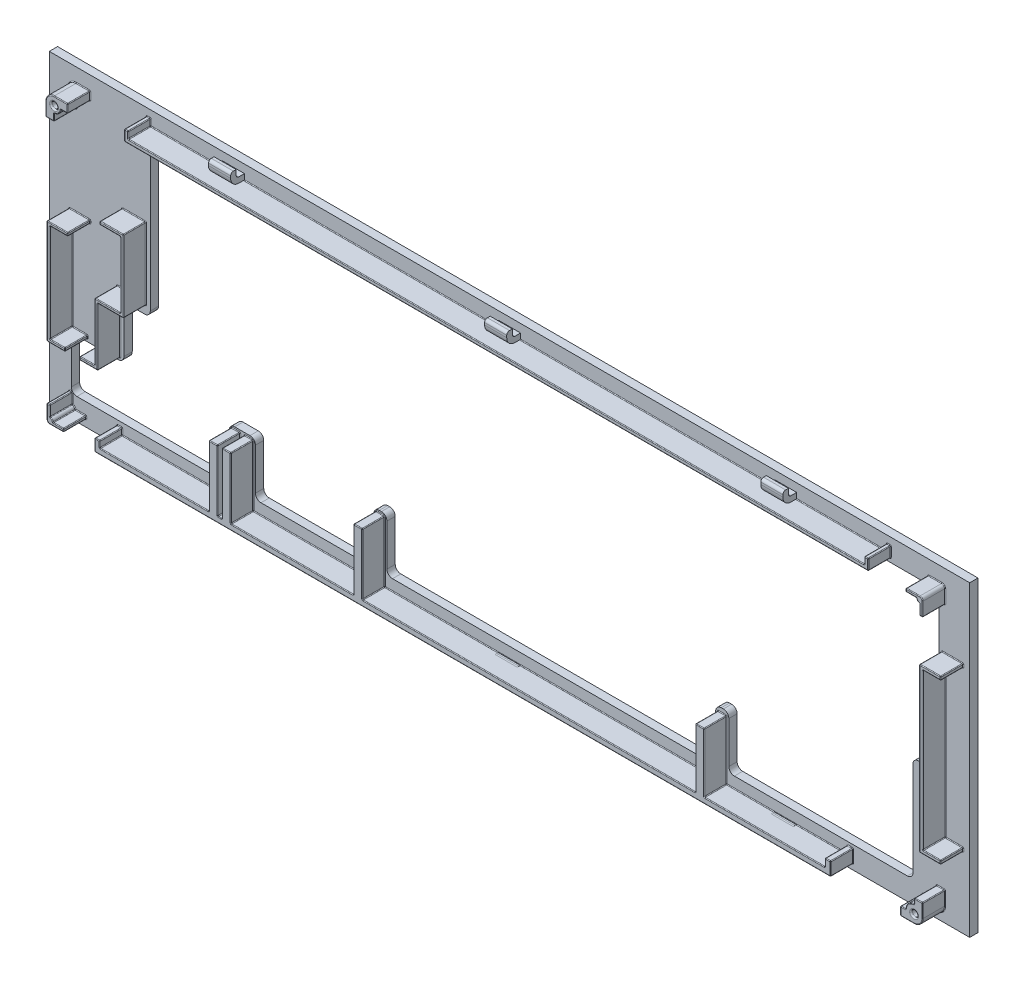
SolidWorks part; units mm, degrees
ref_plane "Front Plane" through (0, 0, 0) normal (0, 0, 1) x (1, 0, 0)
ref_plane "Top Plane" through (0, 0, 0) normal (0, 1, 0) x (1, 0, 0)
ref_plane "Right Plane" through (0, 0, 0) normal (1, 0, 0) x (0, 0, -1)
sketch "keystencil" plane through (0, 0, 0) normal (0, 0, 1) x (1, 0, 0)
  line L0 (-542.8355, 969.3624) -> (-824.5855, 969.3624)
  line L1 (-541.3355, 952.4124) -> (-541.3355, 967.2624) construction
  line L2 (-542.9355, 968.8624) -> (-557.7855, 968.8624) construction
  line L4 (-826.0855, 967.2624) -> (-826.0855, 952.4124) construction
  line L5 (-826.5855, 967.3624) -> (-826.5855, 914.2124)
  line L6 (-819.1605, 911.7124) -> (-834.0105, 911.7124) construction
  line L7 (-828.5855, 912.2124) -> (-834.1105, 912.2124)
  line L8 (-836.1105, 910.2124) -> (-836.1105, 895.1624)
  line L9 (-835.6105, 910.1124) -> (-835.6105, 895.2624) construction
  line L10 (-838.1105, 893.1624) -> (-853.1605, 893.1624)
  line L11 (-838.2105, 892.6624) -> (-853.0605, 892.6624) construction
  line L12 (-854.6605, 891.0624) -> (-854.6605, 876.2124) construction
  line L13 (-855.1605, 891.1624) -> (-855.1605, 876.1124)
  line L14 (-853.1605, 874.1124) -> (-800.0105, 874.1124)
  line L15 (-853.0605, 874.6124) -> (-838.2105, 874.6124) construction
  line L16 (-798.5105, 876.2124) -> (-798.5105, 891.0624) construction
  line L17 (-798.0105, 876.1124) -> (-798.0105, 891.1624)
  line L18 (-796.0105, 893.1624) -> (-790.4855, 893.1624)
  line L19 (-787.9855, 891.0624) -> (-787.9855, 876.2124) construction
  line L20 (-788.4855, 891.1624) -> (-788.4855, 876.1124)
  line L21 (-786.4855, 874.1124) -> (-747.623, 874.1124)
  line L22 (-746.123, 876.2124) -> (-746.123, 891.0624) construction
  line L23 (-767.3355, 874.6124) -> (-747.723, 874.6124) construction
  line L24 (-745.623, 876.1124) -> (-745.623, 891.1624)
  line L25 (-753.048, 893.6624) -> (-738.198, 893.6624) construction
  line L26 (-743.623, 893.1624) -> (-742.8605, 893.1624)
  line L27 (-740.3605, 891.0624) -> (-740.3605, 876.2124) construction
  line L29 (-740.8605, 891.1624) -> (-740.8605, 876.1124)
  line L30 (-738.7605, 874.6124) -> (-623.898, 874.6124) construction
  line L31 (-738.8605, 874.1124) -> (-623.798, 874.1124)
  line L32 (-622.298, 876.2124) -> (-622.298, 891.0624) construction
  line L33 (-621.798, 876.1124) -> (-621.798, 891.1624)
  line L34 (-619.698, 893.6624) -> (-604.848, 893.6624) construction
  line L35 (-619.798, 893.1624) -> (-619.0355, 893.1624)
  line L36 (-616.5355, 891.0624) -> (-616.5355, 876.2124) construction
  line L37 (-617.0355, 891.1624) -> (-617.0355, 876.1124)
  line L38 (-614.9355, 874.6124) -> (-595.323, 874.6124) construction
  line L39 (-615.0355, 874.1124) -> (-552.3605, 874.1124)
  line L40 (-550.8605, 876.2124) -> (-550.8605, 891.0624) construction
  line L41 (-550.3605, 876.1124) -> (-550.3605, 910.2122)
  line L42 (-572.073, 912.7122) -> (-542.9355, 912.7122) construction
  line L43 (-548.3605, 912.2122) -> (-542.8355, 912.2122)
  line L44 (-541.3355, 914.3122) -> (-541.3355, 929.1624) construction
  line L45 (-540.8355, 914.2122) -> (-540.8355, 967.3624)
  line L46 (-814.9605, 893.6624) -> (-776.298, 893.6624) construction
  line L47 (-863.1605, 866.1124) -> (-529.798, 866.1124)
  line L48 (-537.7955, 969.7823) -> (-537.7979, 870.599) construction
  line L49 (-529.798, 866.1124) -> (-529.798, 977.3624)
  line L50 (-529.798, 977.3624) -> (-863.1605, 977.3624)
  line L51 (-863.1605, 977.3624) -> (-863.1605, 866.1124)
  arc A0 (-826.5855, 914.2124) -> (-828.5855, 912.2124) centre (-828.5855, 914.2124) cw
  arc A1 (-836.1105, 910.2124) -> (-834.1105, 912.2124) centre (-834.1105, 910.2124) cw
  arc A2 (-836.1105, 895.1624) -> (-838.1105, 893.1624) centre (-838.1105, 895.1624) cw
  arc A3 (-853.1605, 893.1624) -> (-855.1605, 891.1624) centre (-853.1605, 891.1624) ccw
  arc A4 (-855.1605, 876.1124) -> (-853.1605, 874.1124) centre (-853.1605, 876.1124) ccw
  arc A5 (-800.0105, 874.1124) -> (-798.0105, 876.1124) centre (-800.0105, 876.1124) ccw
  arc A6 (-798.0105, 891.1624) -> (-796.0105, 893.1624) centre (-796.0105, 891.1624) cw
  arc A7 (-790.4855, 893.1624) -> (-788.4855, 891.1624) centre (-790.4855, 891.1624) cw
  arc A8 (-788.4855, 876.1124) -> (-786.4855, 874.1124) centre (-786.4855, 876.1124) ccw
  arc A9 (-747.623, 874.1124) -> (-745.623, 876.1124) centre (-747.623, 876.1124) ccw
  arc A10 (-745.623, 891.1624) -> (-743.623, 893.1624) centre (-743.623, 891.1624) cw
  arc A11 (-740.8605, 891.1624) -> (-742.8605, 893.1624) centre (-742.8605, 891.1624) ccw
  arc A12 (-740.8605, 876.1124) -> (-738.8605, 874.1124) centre (-738.8605, 876.1124) ccw
  arc A13 (-623.798, 874.1124) -> (-621.798, 876.1124) centre (-623.798, 876.1124) ccw
  arc A14 (-621.798, 891.1624) -> (-619.798, 893.1624) centre (-619.798, 891.1624) cw
  arc A15 (-619.0355, 893.1624) -> (-617.0355, 891.1624) centre (-619.0355, 891.1624) cw
  arc A16 (-617.0355, 876.1124) -> (-615.0355, 874.1124) centre (-615.0355, 876.1124) ccw
  arc A17 (-552.3605, 874.1124) -> (-550.3605, 876.1124) centre (-552.3605, 876.1124) ccw
  arc A18 (-550.3605, 910.2122) -> (-548.3605, 912.2122) centre (-548.3605, 910.2122) cw
  arc A19 (-542.8355, 912.2122) -> (-540.8355, 914.2122) centre (-542.8355, 914.2122) ccw
  arc A20 (-540.8355, 967.3624) -> (-542.8355, 969.3624) centre (-542.8355, 967.3624) ccw
  arc A21 (-826.5855, 967.3624) -> (-824.5855, 969.3624) centre (-824.5855, 967.3624) cw
  point P68 (-826.5855, 912.2124)
  point P71 (-836.1105, 912.2124)
  point P74 (-836.1105, 893.1624)
  point P77 (-855.1605, 893.1624)
  point P82 (-798.0105, 874.1124)
  point P87 (-788.4855, 893.1624)
  point P92 (-745.623, 874.1124)
  point P95 (-745.623, 893.1624)
  point P98 (-740.8605, 893.1624)
  point P101 (-740.8605, 874.1124)
  point P104 (-621.798, 874.1124)
  point P107 (-621.798, 893.1624)
  point P110 (-617.0355, 893.1624)
  point P113 (-617.0355, 874.1124)
  point P116 (-550.3605, 874.1124)
  point P119 (-550.3605, 912.2122)
  point P122 (-540.8355, 912.2122)
  point P125 (-540.8355, 969.3624)
  point P128 (-826.5855, 969.3624)
  dimension "D23" = 2
  dimension "D1" = 0.5
  dimension "D2" = 0.5
  dimension "D3" = 0.5
  dimension "D4" = 0.5
  dimension "D5" = 0.5
  dimension "D6" = 0.5
  dimension "D7" = 0.5
  dimension "D8" = 0.5
  dimension "D9" = 0.5
  dimension "D10" = 0.5
  dimension "D11" = 0.5
  dimension "D12" = 0.5
  dimension "D13" = 0.5
  dimension "D14" = 0.5
  dimension "D15" = 0.5
  dimension "D16" = 0.5
  dimension "D17" = 0.5
  dimension "D18" = 0.5
  dimension "D19" = 0.5
  dimension "D20" = 0.5
  dimension "D21" = 0.5
  dimension "D22" = 0.5
  dimension "D24" = 0.5
  dimension "D25" = 8
  dimension "D26" = 8
  dimension "D27" = 8
  dimension "D28" = 8
extrude "faceplate" add sketch "keystencil" along normal blind 3
sketch "platemountsketch" plane through (0, 0, 3) normal (0, 0, 1) x (1, 0, 0)
  line L5 (-856.3455, 964.3319) -> (-853.2955, 964.3319)
  line L6 (-853.2955, 964.3319) -> (-853.2955, 966.9348)
  line L8 (-850.948, 969.2823) -> (-848.3456, 969.2823)
  line L9 (-848.3456, 969.2823) -> (-848.3456, 972.3323)
  line L11 (-538.7455, 876.5322) -> (-541.7955, 876.5322)
  line L13 (-546.7817, 868.4823) -> (-546.7817, 871.5323)
  line L14 (-541.7955, 876.5322) -> (-541.7955, 874.5823)
  line L15 (-546.7817, 871.5323) -> (-544.8455, 871.5323)
  line L23 (-854.823, 868.6216) -> (-849.823, 868.6216)
  line L24 (-849.823, 868.6216) -> (-849.823, 869.7216)
  line L25 (-855.923, 869.7216) -> (-855.923, 874.7216)
  line L26 (-855.923, 874.7216) -> (-854.823, 874.7216)
  line L27 (-849.823, 869.7216) -> (-853.723, 869.7216)
  line L28 (-854.823, 874.7216) -> (-854.823, 870.8216)
  line L35 (-539.817, 972.2049) -> (-544.817, 972.2049)
  line L36 (-544.817, 972.2049) -> (-544.817, 971.1049)
  line L37 (-538.717, 971.1049) -> (-538.717, 966.1049)
  line L38 (-538.717, 966.1049) -> (-539.817, 966.1049)
  line L39 (-544.817, 971.1049) -> (-540.917, 971.1049)
  line L40 (-539.817, 966.1049) -> (-539.817, 970.0049)
  line L41 (-538.7455, 876.5322) -> (-538.7455, 871.5323)
  line L42 (-541.7955, 868.4823) -> (-546.7817, 868.4823)
  line L43 (-856.3455, 969.2823) -> (-856.3455, 964.3319)
  line L44 (-853.2955, 972.3323) -> (-848.3456, 972.3323)
  line L47 (-826.467, 972.2049) -> (-559.798, 972.2049)
  line L48 (-559.798, 970.8073) -> (-826.467, 970.8073)
  line L49 (-529.798, 866.1124) -> (-529.798, 977.3624) construction
  line L50 (-836.7538, 870.1323) -> (-836.7538, 872.4733)
  line L56 (-538.6501, 949.5665) -> (-538.6501, 893.0868)
  line L58 (-539.9001, 949.7709) -> (-539.9001, 893.0868)
  line L60 (-855.923, 895.2571) -> (-855.923, 931.0459)
  line L62 (-854.823, 895.2571) -> (-854.823, 930.7915)
  line L64 (-828.1715, 940.3227) -> (-828.1715, 916.3502)
  line L66 (-829.2701, 940.2675) -> (-829.2701, 916.295)
  line L68 (-837.4684, 915.195) -> (-837.4684, 895.2571)
  line L70 (-838.5684, 915.195) -> (-838.5684, 895.2571)
  line L83 (-836.7538, 872.4733) -> (-838.5684, 872.4733)
  line L84 (-838.5684, 872.4733) -> (-838.5684, 868.0823)
  line L85 (-838.5684, 868.0823) -> (-836.7538, 868.0823)
  line L86 (-574.1069, 870.1323) -> (-574.1069, 872.9022)
  line L87 (-574.1069, 872.9022) -> (-572.0569, 872.9022)
  line L88 (-529.798, 977.3624) -> (-863.1605, 977.3624) construction
  line L89 (-572.0569, 872.9022) -> (-572.0569, 868.0823)
  line L90 (-572.0569, 868.0823) -> (-574.1069, 868.0823)
  line L91 (-788.4855, 891.1624) -> (-788.4855, 876.1124) construction
  line L96 (-798.0105, 876.1124) -> (-798.0105, 891.1624) construction
  line L97 (-863.1605, 977.3624) -> (-863.1605, 866.1124) construction
  line L98 (-836.1105, 910.2124) -> (-836.1105, 895.1624) construction
  line L99 (-826.5855, 967.3624) -> (-826.5855, 914.2124) construction
  line L100 (-836.7538, 868.0823) -> (-574.1069, 868.0823) construction
  line L101 (-574.1069, 870.1323) -> (-574.1069, 868.0823) construction
  line L102 (-836.7538, 870.1323) -> (-574.1069, 870.1323) construction
  line L103 (-836.7538, 870.1323) -> (-836.7538, 868.0823) construction
  line L104 (-797.2105, 892.3624) -> (-797.2105, 869.3323) construction
  line L105 (-794.0505, 869.3323) -> (-797.2105, 869.3323) construction
  line L106 (-794.0505, 892.3624) -> (-794.0505, 869.3323) construction
  line L107 (-794.0505, 892.3624) -> (-797.2105, 892.3624) construction
  line L108 (-789.2855, 892.3624) -> (-789.2855, 869.3323) construction
  line L109 (-789.2855, 869.3323) -> (-792.4455, 869.3323) construction
  line L110 (-792.4455, 892.3624) -> (-792.4455, 869.3323) construction
  line L111 (-789.2855, 892.3624) -> (-792.4455, 892.3624) construction
  line L112 (-741.6605, 892.3624) -> (-741.6605, 869.3323) construction
  line L113 (-741.6605, 869.3323) -> (-744.823, 869.3323) construction
  line L114 (-744.823, 892.3624) -> (-744.823, 869.3323) construction
  line L115 (-741.6605, 892.3624) -> (-744.823, 892.3624) construction
  line L116 (-617.8355, 891.6278) -> (-617.8355, 869.2626) construction
  line L117 (-617.8355, 869.2626) -> (-620.998, 869.2626) construction
  line L118 (-620.998, 891.6278) -> (-620.998, 869.2626) construction
  line L119 (-617.8355, 891.6278) -> (-620.998, 891.6278) construction
  line L120 (-836.7538, 870.1323) -> (-797.2105, 870.1323)
  line L121 (-797.2105, 870.1323) -> (-797.2105, 892.3624)
  line L122 (-797.2105, 892.3624) -> (-794.0505, 892.3624)
  line L123 (-794.0505, 892.3624) -> (-794.0505, 870.1323)
  line L124 (-794.0505, 870.1323) -> (-792.4455, 870.1323)
  line L125 (-792.4455, 870.1323) -> (-792.4455, 892.3624)
  line L126 (-792.4455, 892.3624) -> (-789.2855, 892.3624)
  line L127 (-789.2855, 892.3624) -> (-789.2855, 870.1323)
  line L128 (-789.2855, 870.1323) -> (-744.823, 870.1323)
  line L129 (-744.823, 870.1323) -> (-744.823, 892.3624)
  line L130 (-744.823, 892.3624) -> (-741.6605, 892.3624)
  line L131 (-741.6605, 892.3624) -> (-741.6605, 870.1323)
  line L132 (-741.6605, 870.1323) -> (-620.998, 870.1323)
  line L133 (-620.998, 870.1323) -> (-620.998, 891.6278)
  line L134 (-620.998, 891.6278) -> (-617.8355, 891.6278)
  line L135 (-617.8355, 891.6278) -> (-617.8355, 870.1323)
  line L136 (-617.8355, 870.1323) -> (-574.1069, 870.1323)
  line L138 (-574.1069, 868.0823) -> (-836.7538, 868.0823)
  line L140 (-538.6501, 893.0868) -> (-532.1501, 893.0868)
  line L141 (-532.1501, 893.0868) -> (-532.1501, 891.8368)
  line L142 (-532.1501, 891.8368) -> (-539.9001, 891.8368)
  line L143 (-539.9001, 891.8368) -> (-539.9001, 893.0868)
  line L144 (-538.6501, 949.5665) -> (-532.1501, 949.5665)
  line L145 (-532.1501, 949.5665) -> (-532.1501, 950.8165)
  line L146 (-532.1501, 950.8165) -> (-539.9001, 950.8165)
  line L147 (-539.9001, 950.8165) -> (-539.9001, 949.7709)
  line L148 (-559.798, 972.2049) -> (-559.798, 974.7049)
  line L149 (-559.798, 974.7049) -> (-558.398, 974.7049)
  line L150 (-558.398, 974.7049) -> (-558.398, 970.8073)
  line L151 (-558.398, 970.8073) -> (-559.798, 970.8073)
  line L152 (-826.467, 972.2049) -> (-826.467, 974.7049)
  line L153 (-826.467, 974.7049) -> (-827.867, 974.7049)
  line L154 (-827.867, 974.7049) -> (-827.867, 970.8073)
  line L155 (-827.867, 970.8073) -> (-826.467, 970.8073)
  line L156 (-854.823, 930.7915) -> (-848.323, 930.7915)
  line L157 (-848.323, 930.7915) -> (-848.323, 931.8915)
  line L158 (-848.323, 931.8915) -> (-855.923, 931.8915)
  line L159 (-855.923, 931.8915) -> (-855.923, 931.0459)
  line L160 (-854.823, 895.2571) -> (-849.323, 895.2571)
  line L161 (-849.323, 895.2571) -> (-849.323, 894.1567)
  line L162 (-849.323, 894.1567) -> (-855.923, 894.1567)
  line L163 (-855.923, 894.1567) -> (-855.923, 895.2571)
  line L164 (-838.5684, 895.2571) -> (-844.0684, 895.2571)
  line L165 (-844.0684, 895.2571) -> (-844.0684, 894.1567)
  line L166 (-844.0684, 894.1567) -> (-837.4684, 894.1567)
  line L167 (-837.4684, 894.1567) -> (-837.4684, 895.2571)
  line L168 (-837.4684, 915.195) -> (-828.1715, 915.195)
  line L169 (-828.1715, 915.195) -> (-828.1715, 916.3502)
  line L170 (-829.2701, 916.295) -> (-838.5684, 916.295)
  line L171 (-838.5684, 916.295) -> (-838.5684, 915.195)
  line L172 (-829.2701, 940.2675) -> (-836.7525, 940.2675)
  line L173 (-836.7525, 940.2675) -> (-836.7525, 941.3675)
  line L174 (-836.7525, 941.3675) -> (-828.1715, 941.3675)
  line L175 (-828.1715, 941.3675) -> (-828.1715, 940.3227)
  line L176 (-740.8605, 891.1624) -> (-740.8605, 876.1124) construction
  line L177 (-745.623, 876.1124) -> (-745.623, 891.1624) construction
  line L178 (-617.0355, 891.1624) -> (-617.0355, 876.1124) construction
  line L179 (-621.798, 876.1124) -> (-621.798, 891.1624) construction
  arc A2 (-854.823, 868.6216) -> (-855.923, 869.7216) centre (-854.823, 869.7216) cw
  arc A6 (-856.3455, 969.2823) -> (-853.2955, 972.3323) centre (-853.2955, 969.2823) cw
  arc A10 (-854.823, 870.8216) -> (-853.723, 869.7216) centre (-854.823, 869.7216) cw
  arc A13 (-539.817, 972.2049) -> (-538.717, 971.1049) centre (-539.817, 971.1049) cw
  arc A14 (-539.817, 970.0049) -> (-540.917, 971.1049) centre (-539.817, 971.1049) cw
  arc A19 (-541.7955, 868.4823) -> (-538.7455, 871.5323) centre (-541.7955, 871.5323) ccw
  arc A20 (-544.8455, 871.5323) -> (-541.7955, 874.5823) centre (-541.7955, 871.5323) cw
  arc A21 (-853.2955, 966.9348) -> (-850.948, 969.2823) centre (-853.2955, 969.2823) ccw
  circle A22 centre (-853.2955, 969.2823) radius 1.1
  circle A23 centre (-541.7955, 871.5323) radius 1.1
  dimension "D1" = 1.25
  dimension "D9" = 1.25
  dimension "D4" = 6.5
  dimension "D5" = 5
  dimension "D6" = 5
  dimension "D7" = 5
  dimension "D8" = 5
  dimension "D10" = 6.5
  dimension "D11" = 1.4
  dimension "D12" = 2.5
  dimension "D13" = 1.4
  dimension "D14" = 2.5
  dimension "D15" = 1.1
  dimension "D16" = 1.1
  dimension "D17" = 1.1
  dimension "D18" = 1.1004
  dimension "D19" = 1.1004
  dimension "D20" = 5.5
  dimension "D21" = 1.1
  dimension "D22" = 1.1
  dimension "D23" = 1.1
  dimension "D24" = 5.5
  dimension "D25" = 1.25
  dimension "D26" = 6.5
  dimension "D27" = 8.8522
  dimension "D28" = 5.1575
  dimension "D29" = 1.3976
  dimension "D30" = 7.2375
  dimension "D31" = 1.3579
  dimension "D32" = 1.5861
  dimension "D33" = 42.2589
  dimension "D34" = 24.5921
  dimension "D35" = 0.8
  dimension "D36" = 0.8
  dimension "D37" = 0.8
  dimension "D38" = 0.8
  dimension "D39" = 0.8
  dimension "D40" = 0.8
  dimension "D41" = 2.05
  dimension "D42" = 1.8145
  dimension "D43" = 3.16
  dimension "D44" = 3.16
extrude "platemount" add sketch "platemountsketch" along normal up to surface (8.15 mm away)
fillet "screwholesmooth" radius 0.5 2 edges at (-541.7955, 870.4323, 11.15) (-853.2955, 968.1823, 11.15)
fillet "Fillet1" radius 0.25 42 edges at (-854.8205, 964.3319, 3) (-848.3456, 970.8073, 3) (-854.823, 872.7716, 3) (-849.823, 869.1716, 3) (-852.323, 868.6216, 3) (-538.6501, 921.3267, 11.15) (-540.2705, 876.5322, 3) (-541.7955, 875.5573, 3) (-539.6388, 869.3756, 11.15) (-544.2886, 868.4823, 11.15) (-540.2705, 876.5322, 11.15) (-854.823, 913.0243, 3) (-855.923, 872.2216, 3) (-855.923, 913.0241, 3) (-855.923, 913.0241, 11.15) (-540.5949, 970.3271, 11.15) (-792.4455, 881.2474, 3) (-792.4455, 870.1323, 7.075) (-595.9712, 870.1323, 3) (-705.3126, 868.0823, 3) (-797.2105, 870.1323, 7.075) (-797.2105, 881.2474, 11.15) (-619.4167, 891.6278, 11.15) (-617.8355, 880.8801, 11.15) (-559.098, 974.7049, 3) (-558.398, 970.8073, 7.075) (-826.467, 972.2049, 7.075) (-559.098, 974.7049, 11.15) (-536.0251, 891.8368, 3) (-532.1501, 891.8368, 7.075) (-532.1501, 892.4618, 11.15) (-848.323, 931.8915, 7.075) (-852.623, 894.1567, 3) (-852.123, 931.8915, 11.15) (-848.323, 931.3415, 11.15) (-852.073, 895.2571, 11.15) (-838.5684, 916.295, 7.075) (-828.1715, 941.3675, 7.075) (-836.7525, 940.8175, 11.15) (-573.0819, 872.9022, 3) (-572.0569, 872.9022, 7.075) (-572.0569, 868.0823, 7.075)
ref_plane "midsection" through (-696.478, 0, 0) normal (1, 0, 0) x (0, 0, -1)
sketch "Sketch2" plane through (-696.478, 0, 0) normal (1, 0, 0) x (0, 0, -1)
  line L0 (-3, 974.3624) -> (-5.0527, 974.3624)
  line L1 (-3, 977.3624) -> (-3, 866.1124) construction
  line L3 (-6, 975.3643) -> (-6, 977.1372)
  line L4 (-6, 977.1372) -> (-7, 977.1372)
  line L5 (-8, 976.1372) -> (-8, 975.3643)
  line L7 (-5.0527, 972.3624) -> (-3, 972.3624)
  line L8 (-3, 972.3624) -> (-3, 974.3624)
  line L9 (-3, 867.6124) -> (-5.0635, 867.6124)
  line L10 (-3, 866.1124) -> (-3, 977.3624) construction
  line L11 (-3, 977.3624) -> (0, 977.3624) construction
  line L13 (-7.7843, 866.8899) -> (-5.9634, 869.0944)
  line L16 (-3.6504, 870.184) -> (-3, 870.184)
  line L17 (-3, 870.184) -> (-3, 867.6124)
  arc A0 (-6, 975.3643) -> (-5.0527, 974.3624) centre (-4.9966, 975.3643) ccw
  arc A1 (-5.0527, 972.3624) -> (-8, 975.3643) centre (-5.0527, 975.3102) cw
  arc A2 (-6.0318, 866.8624) -> (-7.7843, 866.8899) centre (-6.8909, 867.9716) cw
  arc A3 (-5.0635, 867.6124) -> (-6.0318, 866.8624) centre (-5.0635, 866.6124) ccw
  arc A4 (-5.9634, 869.0944) -> (-3.6504, 870.184) centre (-3.6504, 867.184) cw
  arc A5 (-8, 976.1372) -> (-7, 977.1372) centre (-7, 976.1372) cw
  point P28 (-8, 977.1372)
  dimension "D5" = 3
  dimension "D6" = 1
  dimension "D1" = 3
  dimension "D2" = 2
  dimension "D3" = 3
  dimension "D4" = 2
extrude "Boss-Extrude1" add sketch "Sketch2" along normal blind 4 and the other way blind 4
pattern_linear "LPattern1" count 2 spacing 100 along (-1, 0, 0) count 2 spacing 100 along (1, 0, 0) of "Boss-Extrude1"
sketch "Sketch3" plane through (0, 0, 0) normal (0, 0, -1) x (-1, 0, 0)
  line L6 (624.2155, 1040.095) -> (624.2155, 1045.4011)
  line L7 (627.2262, 1056.3534) -> (627.2262, 1044.3386)
  line L9 (624.2155, 1060.6148) -> (624.2155, 1055.308)
  line L10 (624.5155, 1055.1348) -> (626.9262, 1056.5266)
  line L11 (624.5164, 1045.5737) -> (626.9252, 1044.1659)
  line L12 (624.2155, 1019.5753) -> (624.2155, 1024.8813)
  line L13 (627.2262, 1035.8337) -> (627.2262, 1023.8189)
  line L14 (624.2155, 1040.095) -> (624.2155, 1034.7883)
  line L15 (624.5155, 1034.6151) -> (626.9262, 1036.0069)
  line L16 (624.5164, 1025.054) -> (626.9252, 1023.6462)
  line L17 (624.2155, 999.0556) -> (624.2155, 1004.3616)
  line L18 (627.2262, 1015.3139) -> (627.2262, 1003.2991)
  line L19 (624.2155, 1019.5753) -> (624.2155, 1014.2685)
  line L20 (624.5155, 1014.0953) -> (626.9262, 1015.4871)
  line L21 (624.5164, 1004.5343) -> (626.9252, 1003.1265)
  line L22 (624.2155, 978.5358) -> (624.2155, 983.8418)
  line L23 (627.2262, 994.7942) -> (627.2262, 982.7794)
  line L24 (624.2155, 999.0556) -> (624.2155, 993.7488)
  line L25 (624.5155, 993.5756) -> (626.9262, 994.9674)
  line L26 (624.5164, 984.0145) -> (626.9252, 982.6067)
  line L27 (624.2155, 958.0161) -> (624.2155, 963.3221)
  line L28 (627.2262, 974.2744) -> (627.2262, 962.2597)
  line L29 (624.2155, 978.5358) -> (624.2155, 973.229)
  line L30 (624.5155, 973.0558) -> (626.9262, 974.4476)
  line L31 (624.5164, 963.4948) -> (626.9252, 962.087)
  line L32 (624.2155, 937.4963) -> (624.2155, 942.8024)
  line L33 (627.2262, 953.7547) -> (627.2262, 941.7399)
  line L34 (624.2155, 958.0161) -> (624.2155, 952.7093)
  line L35 (624.5155, 952.5361) -> (626.9262, 953.9279)
  line L36 (624.5164, 942.975) -> (626.9252, 941.5672)
  line L37 (624.2155, 916.9766) -> (624.2155, 922.2826)
  line L38 (627.2262, 933.235) -> (627.2262, 921.2202)
  line L39 (624.2155, 937.4963) -> (624.2155, 932.1896)
  line L40 (624.5155, 932.0164) -> (626.9262, 933.4082)
  line L41 (624.5164, 922.4553) -> (626.9252, 921.0475)
  line L42 (624.2155, 896.4569) -> (624.2155, 901.7629)
  line L43 (627.2262, 912.7152) -> (627.2262, 900.7004)
  line L44 (624.2155, 916.9766) -> (624.2155, 911.6698)
  line L45 (624.5155, 911.4966) -> (626.9262, 912.8884)
  line L46 (624.5164, 901.9356) -> (626.9252, 900.5278)
  line L47 (624.2155, 875.9371) -> (624.2155, 881.2431)
  line L48 (627.2262, 892.1955) -> (627.2262, 880.1807)
  line L49 (624.2155, 896.4569) -> (624.2155, 891.1501)
  line L50 (624.5155, 890.9769) -> (626.9262, 892.3687)
  line L51 (624.5164, 881.4158) -> (626.9252, 880.008)
  line L52 (624.2155, 855.4174) -> (624.2155, 860.7234)
  line L53 (627.2262, 871.6757) -> (627.2262, 859.6609)
  line L54 (624.2155, 875.9371) -> (624.2155, 870.6303)
  line L55 (624.5155, 870.4571) -> (626.9262, 871.8489)
  line L56 (624.5164, 860.8961) -> (626.9252, 859.4883)
  line L57 (696.478, 31.4533) -> (696.478, -31.4533) construction
  line L108 (624.1155, 1060.6148) -> (624.1155, 1055.308)
  line L109 (624.5655, 1055.0482) -> (626.9762, 1056.44)
  line L110 (627.1262, 1056.3534) -> (627.1262, 1044.3386)
  line L111 (624.5668, 1045.6601) -> (626.9757, 1044.2523)
  line L112 (624.1155, 1040.095) -> (624.1155, 1045.4011)
  line L113 (624.1155, 1040.095) -> (624.1155, 1034.7883)
  line L114 (624.5655, 1034.5285) -> (626.9762, 1035.9203)
  line L115 (627.1262, 1035.8337) -> (627.1262, 1023.8189)
  line L116 (624.5668, 1025.1403) -> (626.9757, 1023.7325)
  line L117 (624.1155, 1019.5753) -> (624.1155, 1024.8813)
  line L118 (624.1155, 1019.5753) -> (624.1155, 1014.2685)
  line L119 (624.5655, 1014.0087) -> (626.9762, 1015.4005)
  line L120 (627.1262, 1015.3139) -> (627.1262, 1003.2991)
  line L121 (624.5668, 1004.6206) -> (626.9757, 1003.2128)
  line L122 (624.1155, 999.0556) -> (624.1155, 1004.3616)
  line L123 (624.1155, 999.0556) -> (624.1155, 993.7488)
  line L124 (624.5655, 993.489) -> (626.9762, 994.8808)
  line L125 (627.1262, 994.7942) -> (627.1262, 982.7794)
  line L126 (624.5668, 984.1009) -> (626.9757, 982.6931)
  line L127 (624.1155, 978.5358) -> (624.1155, 983.8418)
  line L128 (624.1155, 978.5358) -> (624.1155, 973.229)
  line L129 (624.5655, 972.9692) -> (626.9762, 974.361)
  line L130 (627.1262, 974.2744) -> (627.1262, 962.2597)
  line L131 (624.5668, 963.5811) -> (626.9757, 962.1733)
  line L132 (624.1155, 958.0161) -> (624.1155, 963.3221)
  line L133 (624.1155, 958.0161) -> (624.1155, 952.7093)
  line L134 (624.5655, 952.4495) -> (626.9762, 953.8413)
  line L135 (627.1262, 953.7547) -> (627.1262, 941.7399)
  line L136 (624.5668, 943.0614) -> (626.9757, 941.6536)
  line L137 (624.1155, 937.4963) -> (624.1155, 942.8024)
  line L138 (624.1155, 937.4963) -> (624.1155, 932.1896)
  line L139 (624.5655, 931.9298) -> (626.9762, 933.3216)
  line L140 (627.1262, 933.235) -> (627.1262, 921.2202)
  line L141 (624.5668, 922.5416) -> (626.9757, 921.1338)
  line L142 (624.1155, 916.9766) -> (624.1155, 922.2826)
  line L143 (624.1155, 916.9766) -> (624.1155, 911.6698)
  line L144 (624.5655, 911.41) -> (626.9762, 912.8018)
  line L145 (627.1262, 912.7152) -> (627.1262, 900.7004)
  line L146 (624.5668, 902.0219) -> (626.9757, 900.6141)
  line L147 (624.1155, 896.4569) -> (624.1155, 901.7629)
  line L148 (624.1155, 896.4569) -> (624.1155, 891.1501)
  line L149 (624.5655, 890.8903) -> (626.9762, 892.2821)
  line L150 (627.1262, 892.1955) -> (627.1262, 880.1807)
  line L151 (624.5668, 881.5022) -> (626.9757, 880.0944)
  line L152 (624.1155, 875.9371) -> (624.1155, 881.2431)
  line L153 (624.1155, 875.9371) -> (624.1155, 870.6303)
  line L154 (624.5655, 870.3705) -> (626.9762, 871.7623)
  line L155 (627.1262, 871.6757) -> (627.1262, 859.6609)
  line L156 (624.5668, 860.9824) -> (626.9757, 859.5746)
  line L157 (624.1155, 855.4174) -> (624.1155, 860.7234)
  line L208 (624.1155, 1060.6148) -> (624.2155, 1060.6148)
  line L209 (624.1155, 855.4174) -> (624.2155, 855.4174)
  line L210 (768.8405, 855.4174) -> (768.7405, 855.4174)
  line L211 (768.8405, 1060.6148) -> (768.7405, 1060.6148)
  line L212 (768.8405, 855.4174) -> (768.8405, 860.7234)
  line L213 (768.3891, 860.9824) -> (765.9803, 859.5746)
  line L214 (765.8298, 871.6757) -> (765.8298, 859.6609)
  line L215 (768.3905, 870.3705) -> (765.9798, 871.7623)
  line L216 (768.8405, 875.9371) -> (768.8405, 870.6303)
  line L217 (768.8405, 875.9371) -> (768.8405, 881.2431)
  line L218 (768.3891, 881.5022) -> (765.9803, 880.0944)
  line L219 (765.8298, 892.1955) -> (765.8298, 880.1807)
  line L220 (768.3905, 890.8903) -> (765.9798, 892.2821)
  line L221 (768.8405, 896.4569) -> (768.8405, 891.1501)
  line L222 (768.8405, 896.4569) -> (768.8405, 901.7629)
  line L223 (768.3891, 902.0219) -> (765.9803, 900.6141)
  line L224 (765.8298, 912.7152) -> (765.8298, 900.7004)
  line L225 (768.3905, 911.41) -> (765.9798, 912.8018)
  line L226 (768.8405, 916.9766) -> (768.8405, 911.6698)
  line L227 (768.8405, 916.9766) -> (768.8405, 922.2826)
  line L228 (768.3891, 922.5416) -> (765.9803, 921.1338)
  line L229 (765.8298, 933.235) -> (765.8298, 921.2202)
  line L230 (768.3905, 931.9298) -> (765.9798, 933.3216)
  line L231 (768.8405, 937.4963) -> (768.8405, 932.1896)
  line L232 (768.8405, 937.4963) -> (768.8405, 942.8024)
  line L233 (768.3891, 943.0614) -> (765.9803, 941.6536)
  line L234 (765.8298, 953.7547) -> (765.8298, 941.7399)
  line L235 (768.3905, 952.4495) -> (765.9798, 953.8413)
  line L236 (768.8405, 958.0161) -> (768.8405, 952.7093)
  line L237 (768.8405, 958.0161) -> (768.8405, 963.3221)
  line L238 (768.3891, 963.5811) -> (765.9803, 962.1733)
  line L239 (765.8298, 974.2744) -> (765.8298, 962.2597)
  line L240 (768.3905, 972.9692) -> (765.9798, 974.361)
  line L241 (768.8405, 978.5358) -> (768.8405, 973.229)
  line L242 (768.8405, 978.5358) -> (768.8405, 983.8418)
  line L243 (768.3891, 984.1009) -> (765.9803, 982.6931)
  line L244 (765.8298, 994.7942) -> (765.8298, 982.7794)
  line L245 (768.3905, 993.489) -> (765.9798, 994.8808)
  line L246 (768.8405, 999.0556) -> (768.8405, 993.7488)
  line L247 (768.8405, 999.0556) -> (768.8405, 1004.3616)
  line L248 (768.3891, 1004.6206) -> (765.9803, 1003.2128)
  line L249 (765.8298, 1015.3139) -> (765.8298, 1003.2991)
  line L250 (768.3905, 1014.0087) -> (765.9798, 1015.4005)
  line L251 (768.8405, 1019.5753) -> (768.8405, 1014.2685)
  line L252 (768.8405, 1019.5753) -> (768.8405, 1024.8813)
  line L253 (768.3891, 1025.1403) -> (765.9803, 1023.7325)
  line L254 (765.8298, 1035.8337) -> (765.8298, 1023.8189)
  line L255 (768.3905, 1034.5285) -> (765.9798, 1035.9203)
  line L256 (768.8405, 1040.095) -> (768.8405, 1034.7883)
  line L257 (768.8405, 1040.095) -> (768.8405, 1045.4011)
  line L258 (768.3891, 1045.6601) -> (765.9803, 1044.2523)
  line L259 (765.8298, 1056.3534) -> (765.8298, 1044.3386)
  line L260 (768.3905, 1055.0482) -> (765.9798, 1056.44)
  line L261 (768.8405, 1060.6148) -> (768.8405, 1055.308)
  line L262 (768.4396, 860.8961) -> (766.0307, 859.4883)
  line L263 (768.4405, 870.4571) -> (766.0298, 871.8489)
  line L264 (768.7405, 875.9371) -> (768.7405, 870.6303)
  line L265 (765.7298, 871.6757) -> (765.7298, 859.6609)
  line L266 (768.7405, 855.4174) -> (768.7405, 860.7234)
  line L267 (768.4396, 881.4158) -> (766.0307, 880.008)
  line L268 (768.4405, 890.9769) -> (766.0298, 892.3687)
  line L269 (768.7405, 896.4569) -> (768.7405, 891.1501)
  line L270 (765.7298, 892.1955) -> (765.7298, 880.1807)
  line L271 (768.7405, 875.9371) -> (768.7405, 881.2431)
  line L272 (768.4396, 901.9356) -> (766.0307, 900.5278)
  line L273 (768.4405, 911.4966) -> (766.0298, 912.8884)
  line L274 (768.7405, 916.9766) -> (768.7405, 911.6698)
  line L275 (765.7298, 912.7152) -> (765.7298, 900.7004)
  line L276 (768.7405, 896.4569) -> (768.7405, 901.7629)
  line L277 (768.4396, 922.4553) -> (766.0307, 921.0475)
  line L278 (768.4405, 932.0164) -> (766.0298, 933.4082)
  line L279 (768.7405, 937.4963) -> (768.7405, 932.1896)
  line L280 (765.7298, 933.235) -> (765.7298, 921.2202)
  line L281 (768.7405, 916.9766) -> (768.7405, 922.2826)
  line L282 (768.4396, 942.975) -> (766.0307, 941.5672)
  line L283 (768.4405, 952.5361) -> (766.0298, 953.9279)
  line L284 (768.7405, 958.0161) -> (768.7405, 952.7093)
  line L285 (765.7298, 953.7547) -> (765.7298, 941.7399)
  line L286 (768.7405, 937.4963) -> (768.7405, 942.8024)
  line L287 (768.4396, 963.4948) -> (766.0307, 962.087)
  line L288 (768.4405, 973.0558) -> (766.0298, 974.4476)
  line L289 (768.7405, 978.5358) -> (768.7405, 973.229)
  line L290 (765.7298, 974.2744) -> (765.7298, 962.2597)
  line L291 (768.7405, 958.0161) -> (768.7405, 963.3221)
  line L292 (768.4396, 984.0145) -> (766.0307, 982.6067)
  line L293 (768.4405, 993.5756) -> (766.0298, 994.9674)
  line L294 (768.7405, 999.0556) -> (768.7405, 993.7488)
  line L295 (765.7298, 994.7942) -> (765.7298, 982.7794)
  line L296 (768.7405, 978.5358) -> (768.7405, 983.8418)
  line L297 (768.4396, 1004.5343) -> (766.0307, 1003.1265)
  line L298 (768.4405, 1014.0953) -> (766.0298, 1015.4871)
  line L299 (768.7405, 1019.5753) -> (768.7405, 1014.2685)
  line L300 (765.7298, 1015.3139) -> (765.7298, 1003.2991)
  line L301 (768.7405, 999.0556) -> (768.7405, 1004.3616)
  line L302 (768.4396, 1025.054) -> (766.0307, 1023.6462)
  line L303 (768.4405, 1034.6151) -> (766.0298, 1036.0069)
  line L304 (768.7405, 1040.095) -> (768.7405, 1034.7883)
  line L305 (765.7298, 1035.8337) -> (765.7298, 1023.8189)
  line L306 (768.7405, 1019.5753) -> (768.7405, 1024.8813)
  line L307 (768.4396, 1045.5737) -> (766.0307, 1044.1659)
  line L308 (768.4405, 1055.1348) -> (766.0298, 1056.5266)
  line L309 (768.7405, 1060.6148) -> (768.7405, 1055.308)
  line L310 (765.7298, 1056.3534) -> (765.7298, 1044.3386)
  line L311 (768.7405, 1040.095) -> (768.7405, 1045.4011)
  arc A4 (624.2155, 1045.4011) -> (624.5164, 1045.5737) centre (624.4155, 1045.4011) cw
  arc A5 (626.9252, 1044.1659) -> (627.2262, 1044.3386) centre (627.0262, 1044.3386) ccw
  arc A6 (627.2262, 1056.3534) -> (626.9262, 1056.5266) centre (627.0262, 1056.3534) ccw
  arc A7 (624.5155, 1055.1348) -> (624.2155, 1055.308) centre (624.4155, 1055.308) cw
  arc A8 (624.2155, 1024.8813) -> (624.5164, 1025.054) centre (624.4155, 1024.8813) cw
  arc A9 (626.9252, 1023.6462) -> (627.2262, 1023.8189) centre (627.0262, 1023.8189) ccw
  arc A10 (627.2262, 1035.8337) -> (626.9262, 1036.0069) centre (627.0262, 1035.8337) ccw
  arc A11 (624.5155, 1034.6151) -> (624.2155, 1034.7883) centre (624.4155, 1034.7883) cw
  arc A12 (624.2155, 1004.3616) -> (624.5164, 1004.5343) centre (624.4155, 1004.3616) cw
  arc A13 (626.9252, 1003.1265) -> (627.2262, 1003.2991) centre (627.0262, 1003.2991) ccw
  arc A14 (627.2262, 1015.3139) -> (626.9262, 1015.4871) centre (627.0262, 1015.3139) ccw
  arc A15 (624.5155, 1014.0953) -> (624.2155, 1014.2685) centre (624.4155, 1014.2685) cw
  arc A16 (624.2155, 983.8418) -> (624.5164, 984.0145) centre (624.4155, 983.8418) cw
  arc A17 (626.9252, 982.6067) -> (627.2262, 982.7794) centre (627.0262, 982.7794) ccw
  arc A18 (627.2262, 994.7942) -> (626.9262, 994.9674) centre (627.0262, 994.7942) ccw
  arc A19 (624.5155, 993.5756) -> (624.2155, 993.7488) centre (624.4155, 993.7488) cw
  arc A20 (624.2155, 963.3221) -> (624.5164, 963.4948) centre (624.4155, 963.3221) cw
  arc A21 (626.9252, 962.087) -> (627.2262, 962.2597) centre (627.0262, 962.2597) ccw
  arc A22 (627.2262, 974.2744) -> (626.9262, 974.4476) centre (627.0262, 974.2744) ccw
  arc A23 (624.5155, 973.0558) -> (624.2155, 973.229) centre (624.4155, 973.229) cw
  arc A24 (624.2155, 942.8024) -> (624.5164, 942.975) centre (624.4155, 942.8024) cw
  arc A25 (626.9252, 941.5672) -> (627.2262, 941.7399) centre (627.0262, 941.7399) ccw
  arc A26 (627.2262, 953.7547) -> (626.9262, 953.9279) centre (627.0262, 953.7547) ccw
  arc A27 (624.5155, 952.5361) -> (624.2155, 952.7093) centre (624.4155, 952.7093) cw
  arc A28 (624.2155, 922.2826) -> (624.5164, 922.4553) centre (624.4155, 922.2826) cw
  arc A29 (626.9252, 921.0475) -> (627.2262, 921.2202) centre (627.0262, 921.2202) ccw
  arc A30 (627.2262, 933.235) -> (626.9262, 933.4082) centre (627.0262, 933.235) ccw
  arc A31 (624.5155, 932.0164) -> (624.2155, 932.1896) centre (624.4155, 932.1896) cw
  arc A32 (624.2155, 901.7629) -> (624.5164, 901.9356) centre (624.4155, 901.7629) cw
  arc A33 (626.9252, 900.5278) -> (627.2262, 900.7004) centre (627.0262, 900.7004) ccw
  arc A34 (627.2262, 912.7152) -> (626.9262, 912.8884) centre (627.0262, 912.7152) ccw
  arc A35 (624.5155, 911.4966) -> (624.2155, 911.6698) centre (624.4155, 911.6698) cw
  arc A36 (624.2155, 881.2431) -> (624.5164, 881.4158) centre (624.4155, 881.2431) cw
  arc A37 (626.9252, 880.008) -> (627.2262, 880.1807) centre (627.0262, 880.1807) ccw
  arc A38 (627.2262, 892.1955) -> (626.9262, 892.3687) centre (627.0262, 892.1955) ccw
  arc A39 (624.5155, 890.9769) -> (624.2155, 891.1501) centre (624.4155, 891.1501) cw
  arc A40 (624.2155, 860.7234) -> (624.5164, 860.8961) centre (624.4155, 860.7234) cw
  arc A41 (626.9252, 859.4883) -> (627.2262, 859.6609) centre (627.0262, 859.6609) ccw
  arc A42 (627.2262, 871.6757) -> (626.9262, 871.8489) centre (627.0262, 871.6757) ccw
  arc A43 (624.5155, 870.4571) -> (624.2155, 870.6303) centre (624.4155, 870.6303) cw
  arc A84 (624.5655, 1055.0482) -> (624.1155, 1055.308) centre (624.4155, 1055.308) cw
  arc A85 (627.1262, 1056.3534) -> (626.9762, 1056.44) centre (627.0262, 1056.3534) ccw
  arc A86 (626.9757, 1044.2523) -> (627.1262, 1044.3386) centre (627.0262, 1044.3386) ccw
  arc A87 (624.1155, 1045.4011) -> (624.5668, 1045.6601) centre (624.4155, 1045.4011) cw
  arc A88 (624.5655, 1034.5285) -> (624.1155, 1034.7883) centre (624.4155, 1034.7883) cw
  arc A89 (627.1262, 1035.8337) -> (626.9762, 1035.9203) centre (627.0262, 1035.8337) ccw
  arc A90 (626.9757, 1023.7325) -> (627.1262, 1023.8189) centre (627.0262, 1023.8189) ccw
  arc A91 (624.1155, 1024.8813) -> (624.5668, 1025.1403) centre (624.4155, 1024.8813) cw
  arc A92 (624.5655, 1014.0087) -> (624.1155, 1014.2685) centre (624.4155, 1014.2685) cw
  arc A93 (627.1262, 1015.3139) -> (626.9762, 1015.4005) centre (627.0262, 1015.3139) ccw
  arc A94 (626.9757, 1003.2128) -> (627.1262, 1003.2991) centre (627.0262, 1003.2991) ccw
  arc A95 (624.1155, 1004.3616) -> (624.5668, 1004.6206) centre (624.4155, 1004.3616) cw
  arc A96 (624.5655, 993.489) -> (624.1155, 993.7488) centre (624.4155, 993.7488) cw
  arc A97 (627.1262, 994.7942) -> (626.9762, 994.8808) centre (627.0262, 994.7942) ccw
  arc A98 (626.9757, 982.6931) -> (627.1262, 982.7794) centre (627.0262, 982.7794) ccw
  arc A99 (624.1155, 983.8418) -> (624.5668, 984.1009) centre (624.4155, 983.8418) cw
  arc A100 (624.5655, 972.9692) -> (624.1155, 973.229) centre (624.4155, 973.229) cw
  arc A101 (627.1262, 974.2744) -> (626.9762, 974.361) centre (627.0262, 974.2744) ccw
  arc A102 (626.9757, 962.1733) -> (627.1262, 962.2597) centre (627.0262, 962.2597) ccw
  arc A103 (624.1155, 963.3221) -> (624.5668, 963.5811) centre (624.4155, 963.3221) cw
  arc A104 (624.5655, 952.4495) -> (624.1155, 952.7093) centre (624.4155, 952.7093) cw
  arc A105 (627.1262, 953.7547) -> (626.9762, 953.8413) centre (627.0262, 953.7547) ccw
  arc A106 (626.9757, 941.6536) -> (627.1262, 941.7399) centre (627.0262, 941.7399) ccw
  arc A107 (624.1155, 942.8024) -> (624.5668, 943.0614) centre (624.4155, 942.8024) cw
  arc A108 (624.5655, 931.9298) -> (624.1155, 932.1896) centre (624.4155, 932.1896) cw
  arc A109 (627.1262, 933.235) -> (626.9762, 933.3216) centre (627.0262, 933.235) ccw
  arc A110 (626.9757, 921.1338) -> (627.1262, 921.2202) centre (627.0262, 921.2202) ccw
  arc A111 (624.1155, 922.2826) -> (624.5668, 922.5416) centre (624.4155, 922.2826) cw
  arc A112 (624.5655, 911.41) -> (624.1155, 911.6698) centre (624.4155, 911.6698) cw
  arc A113 (627.1262, 912.7152) -> (626.9762, 912.8018) centre (627.0262, 912.7152) ccw
  arc A114 (626.9757, 900.6141) -> (627.1262, 900.7004) centre (627.0262, 900.7004) ccw
  arc A115 (624.1155, 901.7629) -> (624.5668, 902.0219) centre (624.4155, 901.7629) cw
  arc A116 (624.5655, 890.8903) -> (624.1155, 891.1501) centre (624.4155, 891.1501) cw
  arc A117 (627.1262, 892.1955) -> (626.9762, 892.2821) centre (627.0262, 892.1955) ccw
  arc A118 (626.9757, 880.0944) -> (627.1262, 880.1807) centre (627.0262, 880.1807) ccw
  arc A119 (624.1155, 881.2431) -> (624.5668, 881.5022) centre (624.4155, 881.2431) cw
  arc A120 (624.5655, 870.3705) -> (624.1155, 870.6303) centre (624.4155, 870.6303) cw
  arc A121 (627.1262, 871.6757) -> (626.9762, 871.7623) centre (627.0262, 871.6757) ccw
  arc A122 (626.9757, 859.5746) -> (627.1262, 859.6609) centre (627.0262, 859.6609) ccw
  arc A123 (624.1155, 860.7234) -> (624.5668, 860.9824) centre (624.4155, 860.7234) cw
  arc A124 (768.8405, 860.7234) -> (768.3891, 860.9824) centre (768.5405, 860.7234) ccw
  arc A125 (765.9803, 859.5746) -> (765.8298, 859.6609) centre (765.9298, 859.6609) cw
  arc A126 (765.8298, 871.6757) -> (765.9798, 871.7623) centre (765.9298, 871.6757) cw
  arc A127 (768.3905, 870.3705) -> (768.8405, 870.6303) centre (768.5405, 870.6303) ccw
  arc A128 (768.8405, 881.2431) -> (768.3891, 881.5022) centre (768.5405, 881.2431) ccw
  arc A129 (765.9803, 880.0944) -> (765.8298, 880.1807) centre (765.9298, 880.1807) cw
  arc A130 (765.8298, 892.1955) -> (765.9798, 892.2821) centre (765.9298, 892.1955) cw
  arc A131 (768.3905, 890.8903) -> (768.8405, 891.1501) centre (768.5405, 891.1501) ccw
  arc A132 (768.8405, 901.7629) -> (768.3891, 902.0219) centre (768.5405, 901.7629) ccw
  arc A133 (765.9803, 900.6141) -> (765.8298, 900.7004) centre (765.9298, 900.7004) cw
  arc A134 (765.8298, 912.7152) -> (765.9798, 912.8018) centre (765.9298, 912.7152) cw
  arc A135 (768.3905, 911.41) -> (768.8405, 911.6698) centre (768.5405, 911.6698) ccw
  arc A136 (768.8405, 922.2826) -> (768.3891, 922.5416) centre (768.5405, 922.2826) ccw
  arc A137 (765.9803, 921.1338) -> (765.8298, 921.2202) centre (765.9298, 921.2202) cw
  arc A138 (765.8298, 933.235) -> (765.9798, 933.3216) centre (765.9298, 933.235) cw
  arc A139 (768.3905, 931.9298) -> (768.8405, 932.1896) centre (768.5405, 932.1896) ccw
  arc A140 (768.8405, 942.8024) -> (768.3891, 943.0614) centre (768.5405, 942.8024) ccw
  arc A141 (765.9803, 941.6536) -> (765.8298, 941.7399) centre (765.9298, 941.7399) cw
  arc A142 (765.8298, 953.7547) -> (765.9798, 953.8413) centre (765.9298, 953.7547) cw
  arc A143 (768.3905, 952.4495) -> (768.8405, 952.7093) centre (768.5405, 952.7093) ccw
  arc A144 (768.8405, 963.3221) -> (768.3891, 963.5811) centre (768.5405, 963.3221) ccw
  arc A145 (765.9803, 962.1733) -> (765.8298, 962.2597) centre (765.9298, 962.2597) cw
  arc A146 (765.8298, 974.2744) -> (765.9798, 974.361) centre (765.9298, 974.2744) cw
  arc A147 (768.3905, 972.9692) -> (768.8405, 973.229) centre (768.5405, 973.229) ccw
  arc A148 (768.8405, 983.8418) -> (768.3891, 984.1009) centre (768.5405, 983.8418) ccw
  arc A149 (765.9803, 982.6931) -> (765.8298, 982.7794) centre (765.9298, 982.7794) cw
  arc A150 (765.8298, 994.7942) -> (765.9798, 994.8808) centre (765.9298, 994.7942) cw
  arc A151 (768.3905, 993.489) -> (768.8405, 993.7488) centre (768.5405, 993.7488) ccw
  arc A152 (768.8405, 1004.3616) -> (768.3891, 1004.6206) centre (768.5405, 1004.3616) ccw
  arc A153 (765.9803, 1003.2128) -> (765.8298, 1003.2991) centre (765.9298, 1003.2991) cw
  arc A154 (765.8298, 1015.3139) -> (765.9798, 1015.4005) centre (765.9298, 1015.3139) cw
  arc A155 (768.3905, 1014.0087) -> (768.8405, 1014.2685) centre (768.5405, 1014.2685) ccw
  arc A156 (768.8405, 1024.8813) -> (768.3891, 1025.1403) centre (768.5405, 1024.8813) ccw
  arc A157 (765.9803, 1023.7325) -> (765.8298, 1023.8189) centre (765.9298, 1023.8189) cw
  arc A158 (765.8298, 1035.8337) -> (765.9798, 1035.9203) centre (765.9298, 1035.8337) cw
  arc A159 (768.3905, 1034.5285) -> (768.8405, 1034.7883) centre (768.5405, 1034.7883) ccw
  arc A160 (768.8405, 1045.4011) -> (768.3891, 1045.6601) centre (768.5405, 1045.4011) ccw
  arc A161 (765.9803, 1044.2523) -> (765.8298, 1044.3386) centre (765.9298, 1044.3386) cw
  arc A162 (765.8298, 1056.3534) -> (765.9798, 1056.44) centre (765.9298, 1056.3534) cw
  arc A163 (768.3905, 1055.0482) -> (768.8405, 1055.308) centre (768.5405, 1055.308) ccw
  arc A164 (768.4405, 870.4571) -> (768.7405, 870.6303) centre (768.5405, 870.6303) ccw
  arc A165 (765.7298, 871.6757) -> (766.0298, 871.8489) centre (765.9298, 871.6757) cw
  arc A166 (766.0307, 859.4883) -> (765.7298, 859.6609) centre (765.9298, 859.6609) cw
  arc A167 (768.7405, 860.7234) -> (768.4396, 860.8961) centre (768.5405, 860.7234) ccw
  arc A168 (768.4405, 890.9769) -> (768.7405, 891.1501) centre (768.5405, 891.1501) ccw
  arc A169 (765.7298, 892.1955) -> (766.0298, 892.3687) centre (765.9298, 892.1955) cw
  arc A170 (766.0307, 880.008) -> (765.7298, 880.1807) centre (765.9298, 880.1807) cw
  arc A171 (768.7405, 881.2431) -> (768.4396, 881.4158) centre (768.5405, 881.2431) ccw
  arc A172 (768.4405, 911.4966) -> (768.7405, 911.6698) centre (768.5405, 911.6698) ccw
  arc A173 (765.7298, 912.7152) -> (766.0298, 912.8884) centre (765.9298, 912.7152) cw
  arc A174 (766.0307, 900.5278) -> (765.7298, 900.7004) centre (765.9298, 900.7004) cw
  arc A175 (768.7405, 901.7629) -> (768.4396, 901.9356) centre (768.5405, 901.7629) ccw
  arc A176 (768.4405, 932.0164) -> (768.7405, 932.1896) centre (768.5405, 932.1896) ccw
  arc A177 (765.7298, 933.235) -> (766.0298, 933.4082) centre (765.9298, 933.235) cw
  arc A178 (766.0307, 921.0475) -> (765.7298, 921.2202) centre (765.9298, 921.2202) cw
  arc A179 (768.7405, 922.2826) -> (768.4396, 922.4553) centre (768.5405, 922.2826) ccw
  arc A180 (768.4405, 952.5361) -> (768.7405, 952.7093) centre (768.5405, 952.7093) ccw
  arc A181 (765.7298, 953.7547) -> (766.0298, 953.9279) centre (765.9298, 953.7547) cw
  arc A182 (766.0307, 941.5672) -> (765.7298, 941.7399) centre (765.9298, 941.7399) cw
  arc A183 (768.7405, 942.8024) -> (768.4396, 942.975) centre (768.5405, 942.8024) ccw
  arc A184 (768.4405, 973.0558) -> (768.7405, 973.229) centre (768.5405, 973.229) ccw
  arc A185 (765.7298, 974.2744) -> (766.0298, 974.4476) centre (765.9298, 974.2744) cw
  arc A186 (766.0307, 962.087) -> (765.7298, 962.2597) centre (765.9298, 962.2597) cw
  arc A187 (768.7405, 963.3221) -> (768.4396, 963.4948) centre (768.5405, 963.3221) ccw
  arc A188 (768.4405, 993.5756) -> (768.7405, 993.7488) centre (768.5405, 993.7488) ccw
  arc A189 (765.7298, 994.7942) -> (766.0298, 994.9674) centre (765.9298, 994.7942) cw
  arc A190 (766.0307, 982.6067) -> (765.7298, 982.7794) centre (765.9298, 982.7794) cw
  arc A191 (768.7405, 983.8418) -> (768.4396, 984.0145) centre (768.5405, 983.8418) ccw
  arc A192 (768.4405, 1014.0953) -> (768.7405, 1014.2685) centre (768.5405, 1014.2685) ccw
  arc A193 (765.7298, 1015.3139) -> (766.0298, 1015.4871) centre (765.9298, 1015.3139) cw
  arc A194 (766.0307, 1003.1265) -> (765.7298, 1003.2991) centre (765.9298, 1003.2991) cw
  arc A195 (768.7405, 1004.3616) -> (768.4396, 1004.5343) centre (768.5405, 1004.3616) ccw
  arc A196 (768.4405, 1034.6151) -> (768.7405, 1034.7883) centre (768.5405, 1034.7883) ccw
  arc A197 (765.7298, 1035.8337) -> (766.0298, 1036.0069) centre (765.9298, 1035.8337) cw
  arc A198 (766.0307, 1023.6462) -> (765.7298, 1023.8189) centre (765.9298, 1023.8189) cw
  arc A199 (768.7405, 1024.8813) -> (768.4396, 1025.054) centre (768.5405, 1024.8813) ccw
  arc A200 (768.4405, 1055.1348) -> (768.7405, 1055.308) centre (768.5405, 1055.308) ccw
  arc A201 (765.7298, 1056.3534) -> (766.0298, 1056.5266) centre (765.9298, 1056.3534) cw
  arc A202 (766.0307, 1044.1659) -> (765.7298, 1044.3386) centre (765.9298, 1044.3386) cw
  arc A203 (768.7405, 1045.4011) -> (768.4396, 1045.5737) centre (768.5405, 1045.4011) ccw
  point P29 (627.2262, 1056.6998)
  point P482 (765.7298, 1056.6998)
  dimension "D1" = 10
  dimension "D2" = 0.1
